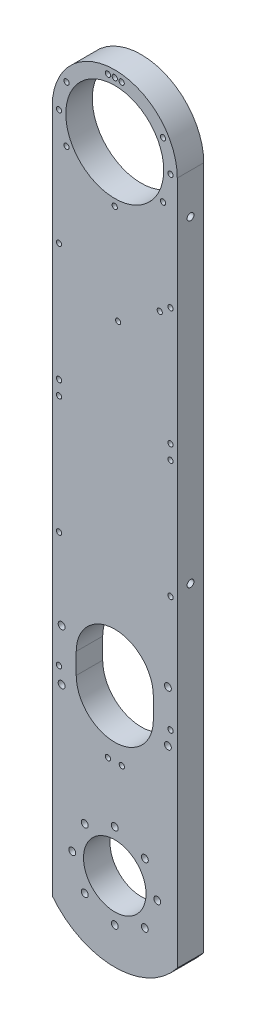
SolidWorks part; units mm, degrees
ref_plane "Front Plane" through (0, 0, 0) normal (0, 0, 1) x (1, 0, 0)
ref_plane "Top Plane" through (0, 0, 0) normal (0, 1, 0) x (1, 0, 0)
ref_plane "Right Plane" through (0, 0, 0) normal (1, 0, 0) x (0, 0, -1)
ref_plane "Plane1" through (0, 0, 12.7) normal (0, 0, 1) x (1, 0, 0)
sketch "Sketch1" plane through (0, 0, 12.7) normal (0, 0, 1) x (1, 0, 0)
  line L0 (-30, 305) -> (-30, 23.3238)
  line L1 (30, 23.3238) -> (30, 305)
  line L2 (30, 23.3238) -> (30, -23.3238)
  line L3 (-30, 23.3238) -> (-30, -23.3238)
  arc A0 (30, 305) -> (-30, 305) centre (0, 305) ccw
  arc A1 (-30, -23.3238) -> (30, -23.3238) centre (0, 0) ccw
extrude "Boss-Extrude1" add sketch "Sketch1" against normal blind 12.7
sketch "Sketch2" plane through (0, 0, 0) normal (0, 0, -1) x (-1, 0, 0)
  line L0 (18.5, 74.0225) -> (18.5, 84.0225)
  line L1 (-18.5, 84.0225) -> (-18.5, 74.0225)
  arc A0 (18.5, 84.0225) -> (-18.5, 84.0225) centre (0, 84.0225) ccw
  arc A1 (-18.5, 74.0225) -> (18.5, 74.0225) centre (0, 74.0225) ccw
extrude "Cut-Extrude1" cut sketch "Sketch2" against normal through all
hole_wizard "Hole1" positions "Sketch4" profile "Sketch3" legacy
sketch "Sketch4" plane through (0, 0, 12.7) normal (0, 0, 1) x (1, 0, 0)
  point P0 (0, 0)
sketch "Sketch3" plane through (0, 0, 12.7) normal (1, 0, 0) x (0, -1, 0)
  line L0 (0, 0) -> (0, 12.7)
  line L1 (0, 12.7) -> (15, 12.7)
  line L2 (15, 12.7) -> (15, 0)
  line L3 (15, 0) -> (0, 0)
  line L4 (0, 110) -> (0, -10) construction
  dimension "Diameter" = 30
  dimension "Depth" = 12.7
hole_wizard "Hole2" positions "Sketch6" profile "Sketch5" legacy
sketch "Sketch6" plane through (0, 0, 12.7) normal (0, 0, 1) x (1, 0, 0)
  point P0 (0, 305)
sketch "Sketch5" plane through (0, 305, 12.7) normal (1, 0, 0) x (0, -1, 0)
  line L0 (0, 0) -> (0, 12.7)
  line L1 (0, 12.7) -> (23.5, 12.7)
  line L2 (23.5, 12.7) -> (23.5, 0)
  line L3 (23.5, 0) -> (0, 0)
  line L4 (0, 110) -> (0, -10) construction
  dimension "Diameter" = 47
  dimension "Depth" = 12.7
hole_wizard "#39 (0.0995) Diameter Hole1" positions "Sketch8" profile "Sketch7" hole size "#39" standard "ANSI Inch"
sketch "Sketch8" plane through (0, 0, 12.7) normal (0, 0, 1) x (1, 0, 0)
  point P0 (-26.75, 74.0225)
  point P1 (-26.75, 129.5112)
  point P2 (-26.75, 186.1112)
  point P3 (-26.75, 192.9112)
  point P4 (-26.75, 249.5112)
  point P5 (-26.75, 305)
  point P6 (-3.3, 331.5457)
  point P7 (3.3, 331.5457)
  point P8 (26.75, 305)
  point P9 (26.75, 249.5112)
  point P10 (26.75, 192.9112)
  point P11 (26.75, 186.1112)
  point P12 (26.75, 129.5112)
  point P13 (26.75, 74.0225)
  point P14 (3.4, 47.4894)
  point P15 (-3.3, 47.4768)
  point P16 (-23.1662, 318.375)
  point P17 (-23.1662, 291.625)
  point P18 (0, 278.25)
  point P19 (23.1662, 291.625)
  point P20 (23.1662, 318.375)
  point P21 (0, 331.75)
sketch "Sketch7" plane through (-26.75, 74.0225, 12.7) normal (1, 0, 0) x (0, -1, 0)
  line L0 (0, 0) -> (0, 12.7)
  line L1 (0, 12.7) -> (1.2636, 12.7)
  line L2 (1.2636, 12.7) -> (1.2636, 0)
  line L5 (1.2636, 0) -> (0, 0)
  line L11 (0, -6.35) -> (0, 107.95) construction
  dimension "Thru Hole Dia." = 2.5273
  dimension "Thru Hole Depth" = 12.7
hole_wizard "#4 Clearance Hole1" positions "Sketch10" profile "Sketch9" hole size "#4" standard "ANSI Inch"
sketch "Sketch10" plane through (0, 0, 0) normal (0, 0, -1) x (-1, 0, 0)
  line L0 (0, 102.5225) -> (0, 55.5225) construction
  arc A0 (18.5, 84.0225) -> (-18.5, 84.0225) centre (0, 84.0225) ccw construction
  arc A1 (-18.5, 74.0225) -> (18.5, 74.0225) centre (0, 74.0225) ccw construction
  point P2 (-25.5016, 66.7725)
  point P3 (-25.5016, 91.2725)
  point P4 (14.425, 14.425)
  point P5 (20.4, 0)
  point P6 (14.425, -14.425)
  point P7 (0, -20.4)
  point P8 (-14.425, -14.425)
  point P9 (-20.4, 0)
  point P10 (-14.425, 14.425)
  point P11 (0, 20.4)
  point P25 (25.5016, 66.7725)
  point P26 (25.5016, 91.2725)
  point P27 (0, 79.0225)
  dimension "D1" = 25.5016
  dimension "D2" = 25.5016
  dimension "D3" = 12.25
  dimension "D4" = 12.25
sketch "Sketch9" plane through (25.5016, 66.7725, 0) normal (1, 0, 0) x (0, 1, 0)
  line L0 (0, 0) -> (0, 12.7)
  line L1 (0, 12.7) -> (1.65, 12.7)
  line L2 (1.65, 12.7) -> (1.65, 0)
  line L5 (1.65, 0) -> (0, 0)
  line L11 (0, -6.35) -> (0, 107.95) construction
  dimension "Thru Hole Dia." = 3.3
  dimension "Thru Hole Depth" = 12.7
hole_wizard "#2 Clearance Hole1" positions "Sketch12" profile "Sketch11" hole size "#2" standard "ANSI Inch"
sketch "Sketch12" plane through (0, 0, 0) normal (0, 0, -1) x (-1, 0, 0)
  point P0 (-1.6199, 231.2653)
  point P1 (-21.5789, 245.4337)
sketch "Sketch11" plane through (1.6199, 231.2653, 0) normal (1, 0, 0) x (0, 1, 0)
  line L0 (0, 0) -> (0, 12.7)
  line L1 (0, 12.7) -> (1.25, 12.7)
  line L2 (1.25, 12.7) -> (1.25, 0)
  line L5 (1.25, 0) -> (0, 0)
  line L11 (0, -6.35) -> (0, 107.95) construction
  dimension "Thru Hole Dia." = 2.5
  dimension "Thru Hole Depth" = 12.7
hole_wizard "#4 Clearance Hole2" positions "Sketch14" profile "Sketch13" hole size "#4" standard "ANSI Inch"
sketch "Sketch14" plane through (30, 0, 0) normal (1, 0, 0) x (0, 0, -1)
  point P0 (-6.35, 285.7238)
  point P1 (-6.35, 133.3238)
sketch "Sketch13" plane through (30, 285.7238, 6.35) normal (0, 1, 0) x (0, 0, -1)
  line L0 (0, 0) -> (0, 10)
  line L1 (0, 10) -> (1.65, 10)
  line L2 (1.65, 10) -> (1.65, 0)
  line L5 (1.65, 0) -> (0, 0)
  line L10 (0, 10) -> (-1.65, 10) construction
  line L11 (0, -6.35) -> (0, 107.95) construction
  dimension "Hole Dia." = 3.3
  dimension "Hole Depth" = 10
  dimension "Drill Angle" = 180
